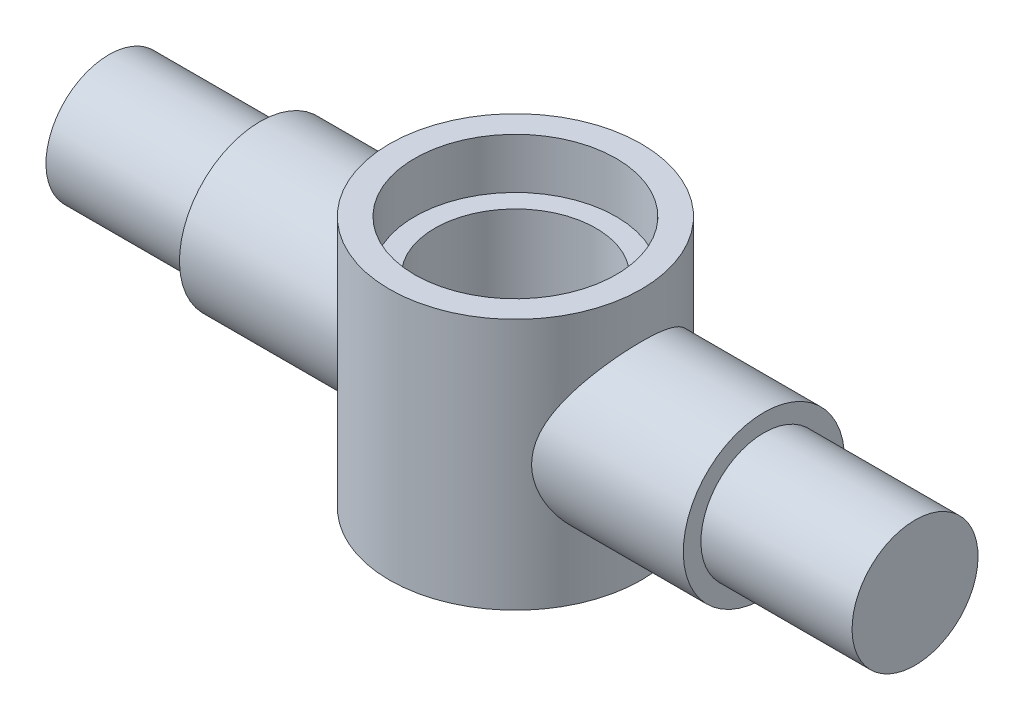
SolidWorks part; units mm, degrees
ref_plane "Front Plane" through (0, 0, 0) normal (0, 0, 1) x (1, 0, 0)
ref_plane "Top Plane" through (0, 0, 0) normal (0, 1, 0) x (1, 0, 0)
ref_plane "Right Plane" through (0, 0, 0) normal (1, 0, 0) x (0, 0, -1)
sketch "Sketch1" plane through (0, 0, 0) normal (0, 0, 1) x (1, 0, 0)
  line L0 (0, 0) -> (0, 50)
  line L1 (0, 50) -> (25, 50)
  line L2 (25, 50) -> (25, 0)
  line L3 (25, 0) -> (0, 0)
  dimension "D1" = 50
  dimension "D2" = 25
revolve "Revolve1" add sketch "Sketch1" angle 360 about L2
sketch "Sketch2" plane through (0, 0, 0) normal (0, 0, 1) x (1, 0, 0)
  line L0 (-55.6782, 25) -> (-55.6782, 37.5)
  line L1 (-55.6782, 37.5) -> (-25.6782, 37.5)
  line L2 (-25.6782, 37.5) -> (-25.6782, 41)
  line L3 (-25.6782, 41) -> (74.3218, 41)
  line L4 (74.3218, 41) -> (74.3218, 37.5)
  line L5 (74.3218, 37.5) -> (104.3218, 37.5)
  line L6 (104.3218, 37.5) -> (104.3218, 25)
  line L7 (104.3218, 25) -> (-55.6782, 25)
  dimension "D1" = 25
  dimension "D2" = 12.5
  dimension "D3" = 16
  dimension "D4" = 160
  dimension "D5" = 100
  dimension "D6" = 55.6782
revolve "Revolve2" add sketch "Sketch2" angle 360 about L7
sketch "Sketch3" plane through (0, 50, 0) normal (0, 1, 0) x (1, 0, 0)
  point P0 (25, 0)
hole_wizard "CBORE for M5 Hex Head Bolt1" positions "Sketch3" profile "Sketch4" counterbore size "M5" standard "ISO" end condition through all
sketch "Sketch4" plane through (25, 50, 0) normal (1, 0, 0) x (0, 0, 1)
  line L0 (0, 0) -> (0, 50)
  line L1 (0, 50) -> (16, 50)
  line L3 (16, 50) -> (16, 10)
  line L4 (16, 10) -> (20, 10)
  line L5 (20, 10) -> (20, 0)
  line L7 (20, 0) -> (0, 0)
  line L11 (0, -6.35) -> (0, 107.95) construction
  dimension "Thru Hole Dia." = 32
  dimension "Thru Hole Depth" = 50
  dimension "C'Bore Dia." = 40
  dimension "C'Bore Depth" = 10
